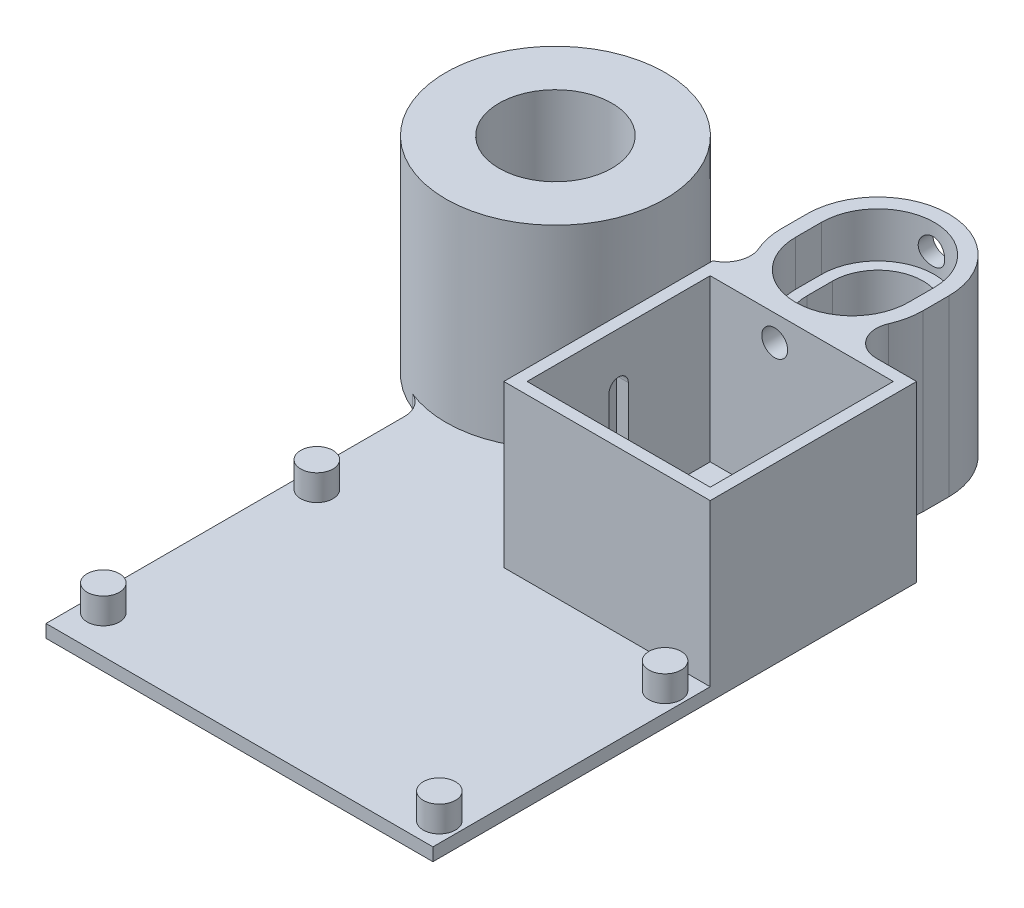
SolidWorks part; units mm, degrees
ref_plane "Front Plane" through (0, 0, 0) normal (0, 0, 1) x (1, 0, 0)
ref_plane "Top Plane" through (0, 0, 0) normal (0, 1, 0) x (1, 0, 0)
ref_plane "Right Plane" through (0, 0, 0) normal (1, 0, 0) x (0, 0, -1)
sketch "Sketch1" plane through (0, 0, 0) normal (0, 1, 0) x (1, 0, 0)
  line L1 (-38.1, -47.625) -> (38.1, -47.625)
  line L2 (-38.1, -47.625) -> (-38.1, 47.625)
  line L3 (-38.1, 47.625) -> (38.1, 47.625)
  line L4 (38.1, -47.625) -> (38.1, 47.625)
  line L5 (-38.1, -47.625) -> (38.1, 47.625) construction
  line L6 (-38.1, 47.625) -> (38.1, -47.625) construction
  point P0 (0, 0)
  dimension "D1" = 95.25
  dimension "D2" = 76.2
extrude "Boss-Extrude1" add sketch "Sketch1" along normal blind 2.54
sketch "Sketch2" plane through (0, 2.54, 0) normal (0, 1, 0) x (1, 0, 0)
  line L1 (38.1, 47.625) -> (-2.54, 47.625)
  line L2 (38.1, 47.625) -> (38.1, 6.985)
  line L3 (38.1, 6.985) -> (-2.54, 6.985)
  line L4 (-2.54, 47.625) -> (-2.54, 6.985)
  dimension "D1" = 40.64
  dimension "D2" = 40.64
extrude "Boss-Extrude2" add sketch "Sketch2" along normal blind 31.75
sketch "Sketch3" plane through (0, 34.29, 0) normal (0, 1, 0) x (1, 0, 0)
  line L0 (-2.54, 47.625) -> (-2.54, 6.985) construction
  line L1 (35.814, 45.339) -> (-0.254, 45.339)
  line L2 (35.814, 45.339) -> (35.814, 9.271)
  line L3 (35.814, 9.271) -> (-0.254, 9.271)
  line L4 (-0.254, 45.339) -> (-0.254, 9.271)
  line L5 (38.1, 47.625) -> (-2.54, 47.625) construction
  line L6 (-2.54, 6.985) -> (38.1, 6.985) construction
  line L7 (38.1, 6.985) -> (38.1, 47.625) construction
  dimension "D1" = 2.286
  dimension "D2" = 2.286
  dimension "D3" = 2.286
  dimension "D4" = 2.286
extrude "Cut-Extrude1" cut sketch "Sketch3" against normal blind 31.75
sketch "Sketch4" plane through (0, 2.54, 0) normal (0, 1, 0) x (1, 0, 0)
  line L0 (38.1, -47.625) -> (38.1, 6.985) construction
  line L1 (-38.1, -47.625) -> (38.1, -47.625) construction
  circle A0 centre (34.29, 1.905) radius 3.175
  circle A1 centre (34.29, -42.545) radius 3.175
  circle A2 centre (-34.29, 1.905) radius 3.175
  circle A3 centre (-34.29, -40.1485) radius 3.175
  dimension "D6" = 6.35
  dimension "D7" = 6.35
  dimension "D8" = 6.35
  dimension "D9" = 6.35
  dimension "D1" = 44.45
  dimension "D2" = 3.81
  dimension "D3" = 5.08
  dimension "D4" = 68.58
  dimension "D5" = 68.58
  dimension "D10" = 3.81
extrude "Boss-Extrude3" add sketch "Sketch4" along normal blind 5.08
sketch "Sketch5" plane through (-2.54, 0, 0) normal (-1, 0, 0) x (0, 0, 1)
  line L0 (-6.985, 34.29) -> (-6.985, 2.54) construction
  line L2 (-29.21, 24.13) -> (-29.21, 5.08)
  line L4 (-25.4, 24.13) -> (-25.4, 5.08)
  line L5 (-47.625, 2.54) -> (-6.985, 2.54) construction
  arc A0 (-25.4, 24.13) -> (-29.21, 24.13) centre (-27.305, 24.13) ccw
  arc A1 (-29.21, 5.08) -> (-25.4, 5.08) centre (-27.305, 5.08) ccw
  dimension "D1" = 19.05
  dimension "D2" = 3.81
  dimension "D3" = 20.32
  dimension "D4" = 2.54
extrude "Cut-Extrude2" cut sketch "Sketch5" against normal up to next
sketch "Sketch6" plane through (0, 2.54, 0) normal (0, 1, 0) x (1, 0, 0)
  line L0 (-2.54, 47.625) -> (-38.1, 47.625) construction
  line L3 (26.67, 60.325) -> (26.67, 65.405)
  line L5 (-1.27, 60.325) -> (-1.27, 65.405)
  arc A0 (-1.27, 60.325) -> (26.67, 60.325) centre (12.7, 60.325) ccw
  arc A1 (26.67, 65.405) -> (-1.27, 65.405) centre (12.7, 65.405) ccw
  dimension "D1" = 27.94
  dimension "D2" = 12.7
  dimension "D3" = 25.4
  dimension "D4" = 27.94
  dimension "D5" = 5.08
extrude "Boss-Extrude4" add sketch "Sketch6" along normal blind 31.75 and the other way blind 2.54
fillet "Fillet1" radius 5.08 2 edges at (18.5199, 17.145, -47.625) (6.8801, 17.145, -47.625)
sketch "Sketch7" plane through (0, 34.29, 0) normal (0, 1, 0) x (1, 0, 0)
  line L2 (21.59, 60.325) -> (21.59, 65.405)
  line L4 (3.81, 60.325) -> (3.81, 65.405)
  arc A0 (3.81, 60.325) -> (21.59, 60.325) centre (12.7, 60.325) ccw
  arc A1 (21.59, 65.405) -> (3.81, 65.405) centre (12.7, 65.405) ccw
  dimension "D1" = 17.78
  dimension "D2" = 17.78
  dimension "D3" = 5.08
extrude "Cut-Extrude3" cut sketch "Sketch7" against normal blind 31.75
sketch "Sketch8" plane through (0, 34.29, 0) normal (0, 1, 0) x (1, 0, 0)
  line L2 (23.8125, 60.325) -> (23.8125, 65.405)
  line L4 (1.5875, 60.325) -> (1.5875, 65.405)
  arc A0 (1.5875, 60.325) -> (23.8125, 60.325) centre (12.7, 60.325) ccw
  arc A2 (23.8125, 65.405) -> (1.5875, 65.405) centre (12.7, 65.405) ccw
  dimension "D1" = 22.225
  dimension "D2" = 5.08
  dimension "D3" = 22.225
extrude "Cut-Extrude4" cut sketch "Sketch8" against normal blind 8.89
sketch "Sketch9" plane through (0, 2.54, 0) normal (0, 1, 0) x (1, 0, 0)
  line L0 (-4.7596, 47.625) -> (-38.1, 47.625) construction
  circle A0 centre (-33.02, 47.625) radius 21.59
  dimension "D1" = 43.18
  dimension "D2" = 0
  dimension "D3" = 5.08
extrude "Boss-Extrude5" add sketch "Sketch9" along normal blind 38.1 and the other way blind 2.54
sketch "Sketch10" plane through (0, 40.64, 0) normal (0, 1, 0) x (1, 0, 0)
  circle A0 centre (-33.02, 47.625) radius 11.1125
  dimension "D1" = 22.225
extrude "Cut-Extrude5" cut sketch "Sketch10" against normal blind 38.1
sketch "Sketch11" plane through (0, 2.54, 0) normal (0, 1, 0) x (1, 0, 0)
  circle A0 centre (12.7, 60.325) radius 3.175
  circle A1 centre (-33.02, 47.625) radius 3.175
  dimension "D1" = 6.35
  dimension "D2" = 6.35
extrude "Cut-Extrude6" cut sketch "Sketch11" against normal up to next
fillet "Fillet2" radius 5.08 2 edges at (-11.43, 1.27, -47.625) (-38.1, 1.27, -26.6412)
sketch "Sketch13" plane through (0, 0, -45.339) normal (0, 0, 1) x (1, 0, 0)
  line L0 (23.8125, 34.29) -> (1.5875, 34.29) construction
  line L3 (-0.254, 2.54) -> (-0.254, 34.29) construction
  circle A0 centre (12.446, 29.21) radius 2.5527
  point P2 (12.7, 34.29)
  dimension "D3" = 5.1054
  dimension "D1" = 5.08
  dimension "D2" = 12.7
extrude "Cut-Extrude7" cut sketch "Sketch13" against normal through all
